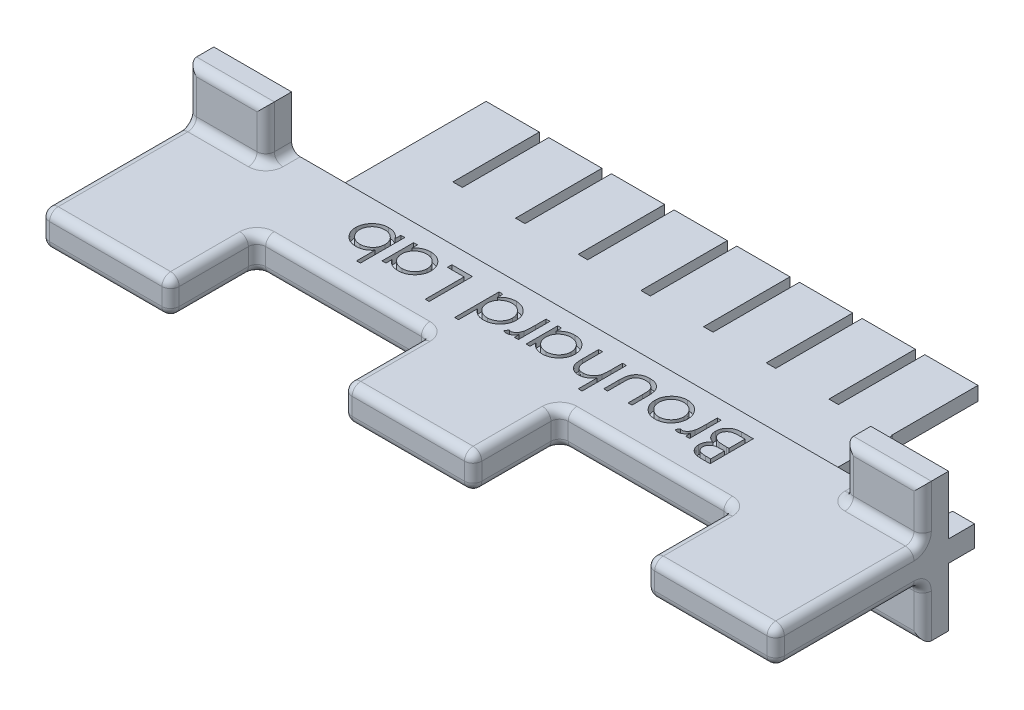
SolidWorks part; units mm, degrees
ref_plane "Front Plane" through (0, 0, 0) normal (0, 0, 1) x (1, 0, 0)
ref_plane "Top Plane" through (0, 0, 0) normal (0, 1, 0) x (1, 0, 0)
ref_plane "Right Plane" through (0, 0, 0) normal (1, 0, 0) x (0, 0, -1)
sketch "Sketch1" plane through (0, 0, 0) normal (0, 0, 1) x (1, 0, 0)
  line L1 (-42.5, 2) -> (42.5, 2)
  line L2 (-42.5, 2) -> (-42.5, -2)
  line L3 (-42.5, -2) -> (42.5, -2)
  line L4 (42.5, 2) -> (42.5, -2)
  line L5 (-42.5, 2) -> (42.5, -2) construction
  line L6 (-42.5, -2) -> (42.5, 2) construction
  point P0 (0, 0)
  dimension "D1" = 85
  dimension "D2" = 4
extrude "Boss-Extrude1" add sketch "Sketch1" along normal blind 10
sketch "Sketch2" plane through (0, 0, 10) normal (0, 0, 1) x (1, 0, 0)
  line L0 (-42.5, -2) -> (42.5, -2) construction
  line L1 (-42.5, 2) -> (-27.5, 2)
  line L2 (-42.5, 2) -> (-42.5, -2)
  line L3 (-42.5, -2) -> (-27.5, -2)
  line L4 (-27.5, 2) -> (-27.5, -2)
  line L6 (42.5, 2) -> (27.5, 2)
  line L7 (42.5, 2) -> (42.5, -2)
  line L8 (42.5, -2) -> (27.5, -2)
  line L9 (27.5, 2) -> (27.5, -2)
  line L10 (-7.5, 2) -> (7.5, 2)
  line L11 (-7.5, 2) -> (-7.5, -2)
  line L12 (-7.5, -2) -> (7.5, -2)
  line L13 (7.5, 2) -> (7.5, -2)
  line L14 (-7.5, 2) -> (7.5, -2) construction
  line L15 (-7.5, -2) -> (7.5, 2) construction
  point P12 (0, 0)
  dimension "D1" = 15
extrude "Boss-Extrude2" add sketch "Sketch2" along normal blind 10
sketch "Sketch3" plane through (0, 0, 0) normal (0, 0, -1) x (-1, 0, 0)
  line L9 (42.5, -1.225) -> (39.95, -1.225)
  line L10 (42.5, -1.225) -> (42.5, 1.225)
  line L11 (42.5, 1.225) -> (39.95, 1.225)
  line L12 (39.95, -1.225) -> (39.95, 1.225)
  line L13 (42.5, -1.225) -> (39.95, 1.225) construction
  line L14 (42.5, 1.225) -> (39.95, -1.225) construction
  line L15 (42.5, 2) -> (42.5, -2) construction
  line L16 (0, 0) -> (0, 13.9589)
  line L17 (-42.5, 1.225) -> (-39.95, -1.225) construction
  line L18 (-42.5, -1.225) -> (-39.95, 1.225) construction
  line L19 (-39.95, -1.225) -> (-39.95, 1.225)
  line L20 (-42.5, 1.225) -> (-39.95, 1.225)
  line L21 (-42.5, -1.225) -> (-42.5, 1.225)
  line L22 (-42.5, -1.225) -> (-39.95, -1.225)
  point P3 (42.5, 0)
  point P10 (41.225, 0)
  point P16 (-41.225, 0)
  line M3 (-42.5, 2) -> (-42.5, -2)
  dimension "D1" = 2.45
  dimension "D2" = 2.55
extrude "Boss-Extrude3" add sketch "Sketch3" along normal blind 3 contours L22 L19 L20 M3 | L12 L11 L10 L9
sketch "Sketch4" plane through (0, 0, 0) normal (0, 0, -1) x (-1, 0, 0)
  line L1 (28.5, -0.8) -> (-28.5, -0.8)
  line L2 (28.5, -0.8) -> (28.5, 0.8)
  line L3 (28.5, 0.8) -> (-28.5, 0.8)
  line L4 (-28.5, -0.8) -> (-28.5, 0.8)
  line L5 (28.5, -0.8) -> (-28.5, 0.8) construction
  line L6 (28.5, 0.8) -> (-28.5, -0.8) construction
  point P0 (0, 0)
  dimension "D1" = 1.6
  dimension "D2" = 57
extrude "Boss-Extrude4" add sketch "Sketch4" along normal blind 7.5
sketch "Sketch6" plane through (0, 0, 0) normal (0, 0, -1) x (-1, 0, 0)
  line L1 (42.5, -2) -> (33.5, -2)
  line L2 (42.5, -2) -> (42.5, -8)
  line L3 (42.5, -8) -> (33.5, -8)
  line L4 (33.5, -2) -> (33.5, -8)
  line L5 (42.5, 2) -> (33.5, 2)
  line L6 (42.5, 2) -> (42.5, 8)
  line L7 (42.5, 8) -> (33.5, 8)
  line L8 (33.5, 2) -> (33.5, 8)
  line L9 (-42.5, -2) -> (-33.5, -2)
  line L10 (-42.5, -2) -> (-42.5, -8)
  line L11 (-42.5, -8) -> (-33.5, -8)
  line L12 (-33.5, -2) -> (-33.5, -8)
  line L13 (-42.5, 2) -> (-33.5, 2)
  line L14 (-42.5, 2) -> (-42.5, 8)
  line L15 (-42.5, 8) -> (-33.5, 8)
  line L16 (-33.5, 2) -> (-33.5, 8)
  dimension "D1" = 6
  dimension "D2" = 9
extrude "Boss-Extrude6" add sketch "Sketch6" against normal blind 3
fillet "Fillet1" radius 1 52 edges at (-42.5, -2, 11.5) (-33.5, -2, 1.5) (-38, -2, 3) (-33.5, -5, 3) (-38, -8, 3) (-42.5, -5, 3) (-27.5, 0, 20) (-35, -2, 20) (-42.5, 0, 20) (-35, 2, 20) (33.5, -2, 1.5) (42.5, -2, 11.5) (42.5, 2, 11.5) (33.5, 2, 1.5) (-33.5, 2, 1.5) (-42.5, 2, 11.5) (38, -8, 3) (33.5, -5, 3) (38, -2, 3) (42.5, -5, 3) (35, -2, 20) (27.5, 0, 20) (35, 2, 20) (42.5, 0, 20) (38, 2, 3) (33.5, 5, 3) (38, 8, 3) (42.5, 5, 3) (0, -2, 20) (-7.5, 0, 20) (0, 2, 20) (7.5, 0, 20) (-38, 8, 3) (-33.5, 5, 3) (-38, 2, 3) (-42.5, 5, 3) (27.5, 2, 15) (27.5, -2, 15) (27.5, 0, 10) (17.5, -2, 10) (17.5, 2, 10) (7.5, -2, 15) (7.5, 2, 15) (7.5, 0, 10) (-7.5, 2, 15) (-7.5, -2, 15) (-27.5, -2, 15) (-27.5, 2, 15) (-27.5, 0, 10) (-17.5, 2, 10) (-7.5, 0, 10) (-17.5, -2, 10)
ref_plane "Plane1" through (0, 0, 0) normal (0, 1, 0) x (1, 0, 0)
sketch "Sketch7" plane through (0, 2, 0) normal (0, 1, 0) x (1, 0, 0)
  line L0 (30.9142, -2.045) -> (-30.9142, -2.045)
  line L1 (32.5, 0) -> (-32.5, 0) construction
  point P2 (0, -2.045)
  point P5 (0, 0)
sketch "Sketch8" plane through (0, 2, 0) normal (0, 1, 0) x (1, 0, 0)
  text T0 "Brouhard Lab" font "Century Gothic" height 5
extrude "Cut-Extrude1" cut sketch "Sketch8" against normal blind 1
sketch "Sketch5" plane through (0, 0, -7.5) normal (0, 0, -1) x (-1, 0, 0)
  line L0 (28.5, 0.8) -> (-28.5, 0.8) construction
  line L1 (28.5, -0.8) -> (22.35, -0.8)
  line L2 (28.5, -0.8) -> (28.5, 0.8)
  line L3 (28.5, 0.8) -> (22.35, 0.8)
  line L4 (22.35, -0.8) -> (22.35, 0.8)
  line L97 (21.25, -0.8) -> (15.1, -0.8)
  line L98 (21.25, -0.8) -> (21.25, 0.8)
  line L99 (21.25, 0.8) -> (15.1, 0.8)
  line L100 (15.1, -0.8) -> (15.1, 0.8)
  line L101 (14, -0.8) -> (7.85, -0.8)
  line L102 (14, -0.8) -> (14, 0.8)
  line L103 (14, 0.8) -> (7.85, 0.8)
  line L104 (7.85, -0.8) -> (7.85, 0.8)
  line L105 (6.75, -0.8) -> (0.6, -0.8)
  line L106 (6.75, -0.8) -> (6.75, 0.8)
  line L107 (6.75, 0.8) -> (0.6, 0.8)
  line L108 (0.6, -0.8) -> (0.6, 0.8)
  line L109 (-0.5, -0.8) -> (-6.65, -0.8)
  line L110 (-0.5, -0.8) -> (-0.5, 0.8)
  line L111 (-0.5, 0.8) -> (-6.65, 0.8)
  line L112 (-6.65, -0.8) -> (-6.65, 0.8)
  line L113 (-7.75, -0.8) -> (-13.9, -0.8)
  line L114 (-7.75, -0.8) -> (-7.75, 0.8)
  line L115 (-7.75, 0.8) -> (-13.9, 0.8)
  line L116 (-13.9, -0.8) -> (-13.9, 0.8)
  line L117 (-15, -0.8) -> (-21.15, -0.8)
  line L118 (-15, -0.8) -> (-15, 0.8)
  line L119 (-15, 0.8) -> (-21.15, 0.8)
  line L120 (-21.15, -0.8) -> (-21.15, 0.8)
  line L121 (-22.25, -0.8) -> (-28.4, -0.8)
  line L122 (-22.25, -0.8) -> (-22.25, 0.8)
  line L123 (-22.25, 0.8) -> (-28.4, 0.8)
  line L124 (-28.4, -0.8) -> (-28.4, 0.8)
  dimension "D2" = 6.15
  dimension "D1" = 8
extrude "Boss-Extrude5" add sketch "Sketch5" along normal blind 10
